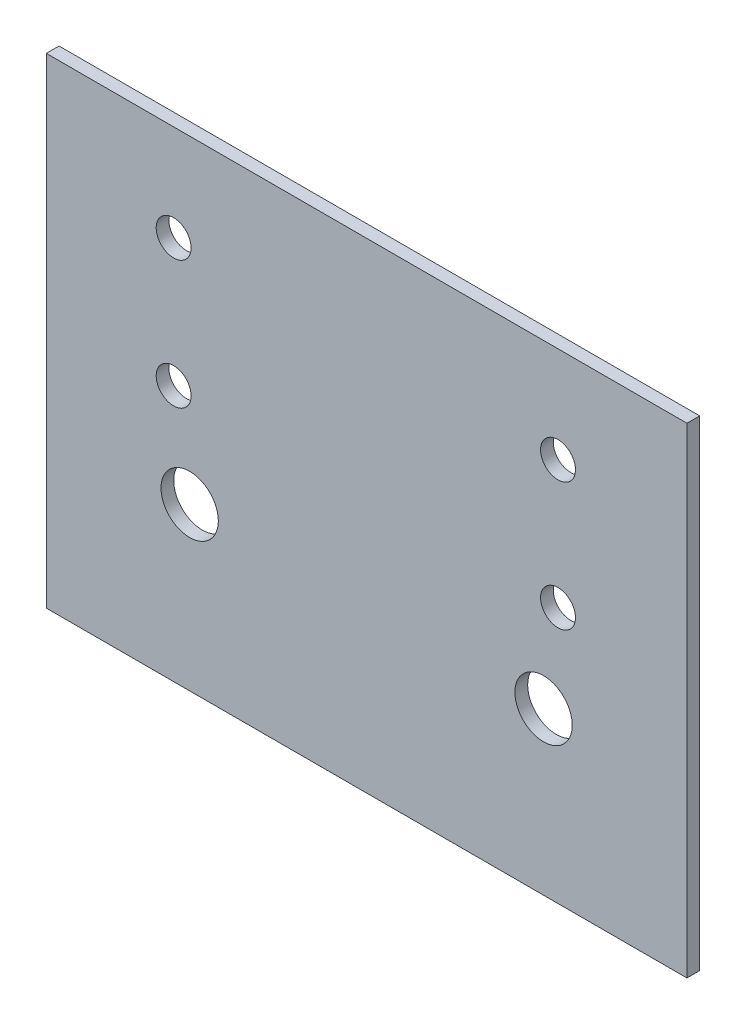
SolidWorks part; units mm, degrees
ref_plane "前视基准面" through (0, 0, 0) normal (0, 0, 1) x (1, 0, 0)
ref_plane "上视基准面" through (0, 0, 0) normal (0, 1, 0) x (1, 0, 0)
ref_plane "右视基准面" through (0, 0, 0) normal (1, 0, 0) x (0, 0, -1)
sketch "草图1" plane through (0, 0, 0) normal (0, 0, 1) x (1, 0, 0)
  line L0 (-55.414, 34.3937) -> (346.8207, 34.3937)
  line L1 (-55.414, 34.3937) -> (-55.414, -267.2823)
  line L2 (-55.414, -267.2823) -> (346.8207, -267.2823)
  line L3 (346.8207, -267.2823) -> (346.8207, 34.3937)
  circle A0 centre (24.5342, -25.9415) radius 10.9609
  circle A1 centre (265.875, -25.9415) radius 10.9609
  circle A8 centre (24.5342, -106.3884) radius 10.9609
  circle A9 centre (265.875, -106.3884) radius 10.9609
  circle A12 centre (34.59, -165.8797) radius 18
  circle A13 centre (256.8167, -165.8797) radius 18
  dimension "D1" = 36
  dimension "D2" = 36
extrude "凸台-拉伸1" add sketch "草图1" along normal blind 8
sketch "草图2" plane through (0, 0, 0) normal (0, 0, 1) x (1, 0, 0)
